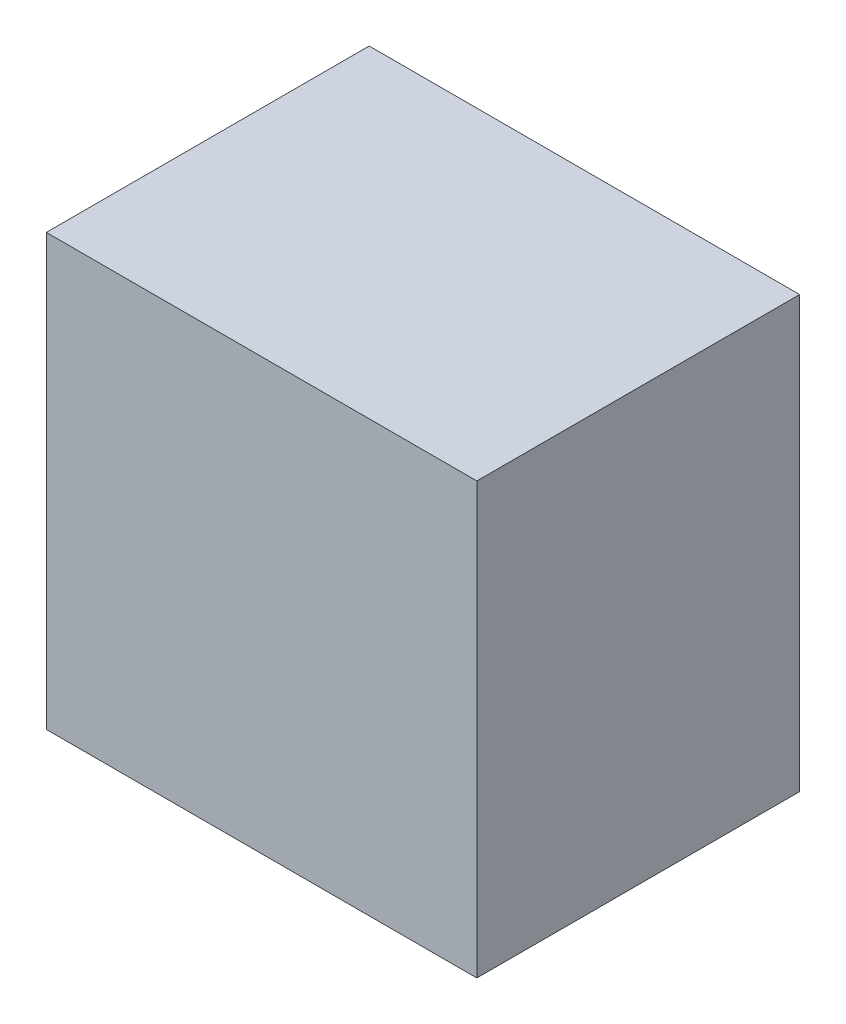
SolidWorks part; units mm, degrees
ref_plane "Front Plane" through (0, 0, 0) normal (0, 0, 1) x (1, 0, 0)
ref_plane "Top Plane" through (0, 0, 0) normal (0, 1, 0) x (1, 0, 0)
ref_plane "Right Plane" through (0, 0, 0) normal (1, 0, 0) x (0, 0, -1)
sketch "Sketch1" plane through (0, 0, 0) normal (0, 1, 0) x (1, 0, 0)
  line L1 (0, 0) -> (25.4, 0)
  line L2 (0, 0) -> (0, 19.05)
  line L3 (0, 19.05) -> (25.4, 19.05)
  line L4 (25.4, 0) -> (25.4, 19.05)
  dimension "D1" = 25.4
  dimension "D2" = 19.05
extrude "Boss-Extrude1" add sketch "Sketch1" along normal blind 25.4
